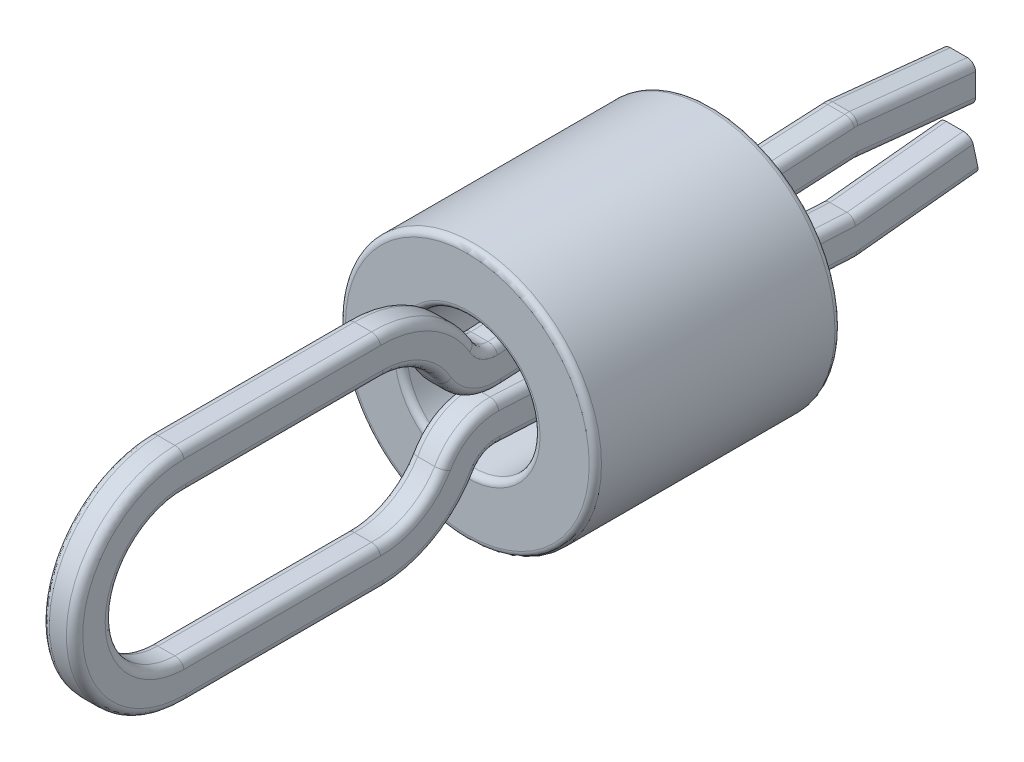
SolidWorks part; units mm, degrees
ref_plane "Front Plane" through (0, 0, 0) normal (0, 0, 1) x (1, 0, 0)
ref_plane "Top Plane" through (0, 0, 0) normal (0, 1, 0) x (1, 0, 0)
ref_plane "Right Plane" through (0, 0, 0) normal (1, 0, 0) x (0, 0, -1)
sketch "Sketch1" plane through (0, 0, 0) normal (0, 0, 1) x (1, 0, 0)
  circle A0 centre (0, 0) radius 1.5875
  circle A1 centre (0, 0) radius 0.8255
  dimension "D1" = 3.175
  dimension "D2" = 1.651
extrude "Plastic-Ring" add sketch "Sketch1" along normal blind 3.048
fillet "Fillet1" radius 0.0762 4 edges at (0.8255, 0, 0) (1.5875, 0, 0) (0.8255, 0, 3.048) (1.5875, 0, 3.048)
sketch "wire-bend" plane through (0, 0, 0) normal (1, 0, 0) x (0, 0, -1)
  line L0 (-9.1256, 0) -> (4.6063, 0) construction
  line L1 (1.565, -0.5329) -> (-2.8601, -0.3048)
  line L2 (3.048, 0.381) -> (1.5846, 0.5324)
  line L3 (-4.318, -2.4535) -> (-4.318, 2.2891) construction
  line L4 (1.565, 0.5329) -> (-2.8601, 0.3048)
  line L5 (-4.318, 1.1303) -> (-6.7564, 1.1303)
  line L6 (-6.7564, -2.4535) -> (-6.7564, 2.2891) construction
  line L7 (3.048, -0.381) -> (1.5846, -0.5324)
  line L8 (-4.318, -1.1303) -> (-6.7564, -1.1303)
  arc A0 (-4.318, 1.1303) -> (-3.3391, 0.5651) centre (-4.318, 0) cw
  arc A1 (-3.3391, 0.5651) -> (-2.8601, 0.3048) centre (-2.887, 0.8262) ccw
  arc A2 (1.5846, 0.5324) -> (1.565, 0.5329) centre (1.5715, 0.4061) ccw
  arc A3 (1.5846, -0.5324) -> (1.565, -0.5329) centre (1.5715, -0.4061) cw
  arc A4 (-6.7564, 1.1303) -> (-6.7564, -1.1303) centre (-6.7564, 0) ccw
  arc A5 (-3.3391, -0.5651) -> (-2.8601, -0.3048) centre (-2.887, -0.8262) cw
  arc A6 (-4.318, -1.1303) -> (-3.3391, -0.5651) centre (-4.318, 0) ccw
  point P12 (-2.8956, 0.3175)
  point P15 (1.5748, 0.5334)
  point P23 (1.5748, -0.5334)
  point P24 (-2.8956, -0.3175)
  dimension "D9" = 6.7564
  dimension "D2" = 1.1303
  dimension "D1" = 4.318
  dimension "D3" = 0.381
  dimension "D4" = 3.048
  dimension "D5" = 1.5748
  dimension "D6" = 0.5334
  dimension "D7" = 0.3048
  dimension "D8" = 2.8956
  dimension "D11" = 60
ref_plane "Plane1" through (0, 0, -3.048) normal (0, 0, 1) x (1, 0, 0)
sketch "wire-profile" plane through (0, 0, -3.048) normal (0, 0, 1) x (1, 0, 0)
  line L1 (-0.1054, 0.6223) -> (0.1054, 0.6223)
  line L2 (-0.207, 0.5207) -> (-0.207, 0.2413)
  line L3 (-0.1054, 0.1397) -> (0.1054, 0.1397)
  line L4 (0.207, 0.5207) -> (0.207, 0.2413)
  line L5 (-0.207, 0.6223) -> (0.207, 0.1397) construction
  line L6 (-0.207, 0.1397) -> (0.207, 0.6223) construction
  arc A0 (0.1054, 0.6223) -> (0.207, 0.5207) centre (0.1054, 0.5207) cw
  arc A1 (0.1054, 0.1397) -> (0.207, 0.2413) centre (0.1054, 0.2413) ccw
  arc A2 (-0.207, 0.2413) -> (-0.1054, 0.1397) centre (-0.1054, 0.2413) ccw
  arc A3 (-0.1054, 0.6223) -> (-0.207, 0.5207) centre (-0.1054, 0.5207) ccw
  point P0 (0, 0.381)
  dimension "D3" = 0.1016
  dimension "D1" = 0.4826
  dimension "D2" = 0.414
sweep "Sweep3" add profiles "wire-profile" path "wire-bend"
ref_plane "Plane2" through (0, 0, -1.5748) normal (0, 0, 1) x (1, 0, 0)
sketch "VIA hole" plane through (0, 0, -1.5748) normal (0, 0, 1) x (1, 0, 0)
  circle A0 centre (0, 0) radius 0.8001 construction
  circle A1 centre (0, 0) radius 0.8255 construction
  dimension "D1" = 1.6002
  dimension "D2" = 0.0254
